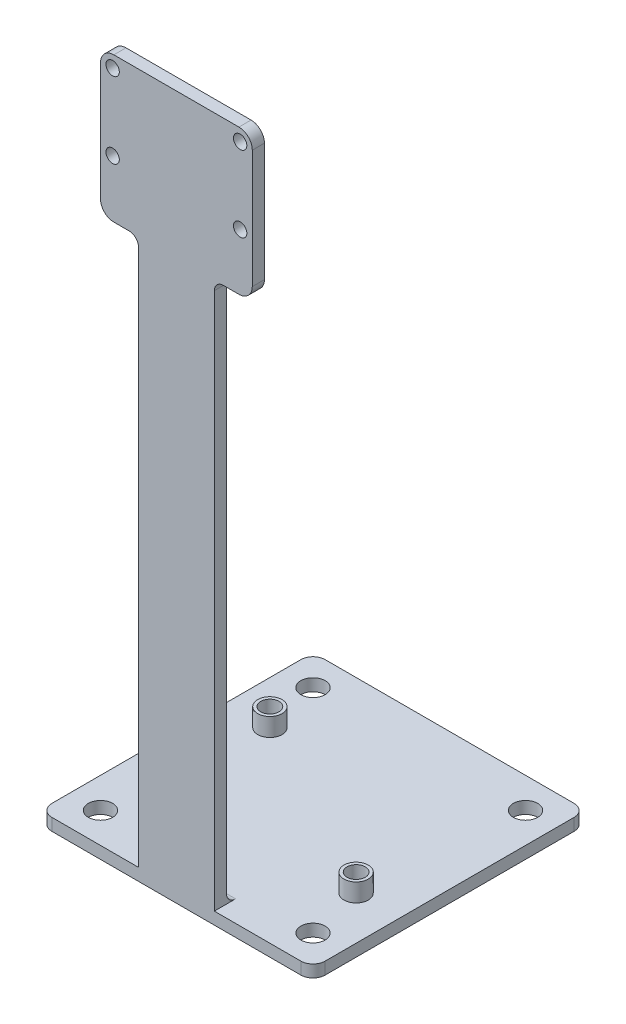
SolidWorks part; units mm, degrees
ref_plane "Front Plane" through (0, 0, 0) normal (0, 0, 1) x (1, 0, 0)
ref_plane "Top Plane" through (0, 0, 0) normal (0, 1, 0) x (1, 0, 0)
ref_plane "Right Plane" through (0, 0, 0) normal (1, 0, 0) x (0, 0, -1)
sketch "Sketch1" plane through (0, 0, 0) normal (0, 0, 1) x (1, 0, 0)
  line L0 (6.25, 0) -> (6.25, -90)
  line L1 (0, 0) -> (6.25, 0)
  line L2 (0, 0) -> (0, 23.862)
  line L3 (0, 23.862) -> (25, 23.862)
  line L4 (25, 0) -> (25, 23.862)
  line L5 (18.75, 0) -> (18.75, -90)
  line L6 (18.75, 0) -> (25, 0)
  line L7 (6.25, -90) -> (18.75, -90)
  circle A2 centre (2, 21.862) radius 1.1
  circle A3 centre (23, 21.862) radius 1.1
  circle A4 centre (2, 9.362) radius 1.1
  circle A5 centre (23, 9.362) radius 1.1
  dimension "D3" = 2.2
  dimension "D4" = 2.2
  dimension "D7" = 2.2
  dimension "D10" = 2.2
  dimension "D1" = 25
  dimension "D2" = 23.862
  dimension "D5" = 2
  dimension "D6" = 2
  dimension "D8" = 2
  dimension "D9" = 2
  dimension "D11" = 14.5
  dimension "D12" = 90
  dimension "D13" = 90
  dimension "D14" = 12.5
  dimension "D15" = 6.25
extrude "Boss-Extrude1" add sketch "Sketch1" along normal blind 2
fillet "Fillet1" radius 2.2 1 edges at (0, 0, 1)
fillet "Fillet2" radius 2.2 1 edges at (0, 23.862, 1)
fillet "Fillet3" radius 2.2 1 edges at (25, 23.862, 1)
fillet "Fillet5" radius 2.2 1 edges at (25, 0, 1)
fillet "Fillet6" radius 1.5 1 edges at (18.75, 0, 1)
fillet "Fillet7" radius 1.5 1 edges at (6.25, 0, 1)
sketch "Sketch5" plane through (0, -90, 0) normal (0, -1, 0) x (1, 0, 0)
  line L0 (6.25, 2) -> (6.25, 0) construction
  line L1 (-10, 2) -> (35, 2)
  line L2 (-10, 2) -> (-10, -43)
  line L3 (-10, -43) -> (35, -43)
  line L4 (35, 2) -> (35, -43)
  line L5 (6.25, 0) -> (18.75, 0) construction
  line L6 (6.25, 2) -> (18.75, 2) construction
  circle A0 centre (-5, -3) radius 2
  circle A1 centre (-5, -38) radius 2
  circle A2 centre (30, -3) radius 2
  circle A3 centre (30, -38) radius 2
  point P4 (-10, -20.5)
  point P5 (35, -20.5)
  point P6 (12.5, 2)
  point P7 (0, 0)
  point P8 (6.25, 1)
  point P9 (12.5, 0)
  point P16 (0, 0)
  point P23 (0, 0)
  point P24 (0, 0)
  point P25 (0, 0)
  point P26 (12.9667, -5.2821)
  point P27 (17.2186, -7.336)
  point P28 (0, 0)
  point P29 (0, 0)
  point P30 (0, 0)
  point P33 (0, 0)
  point P34 (0, 0)
  point P35 (0, 0)
  point P36 (12.5, 2)
  point P37 (0, 0)
  dimension "D4" = 4
  dimension "D5" = 4
  dimension "D6" = 4
  dimension "D7" = 4
  dimension "D1" = 45
  dimension "D2" = 45
  dimension "D3" = 35
  dimension "D8" = 35
  dimension "D9" = 5
  dimension "D10" = 5
extrude "Boss-Extrude4" add sketch "Sketch5" along normal blind 2
fillet "Fillet17" radius 2 1 edges at (35, -91, 2)
fillet "Fillet18" radius 2 1 edges at (-10, -91, 2)
fillet "Fillet19" radius 2 1 edges at (-10, -91, -43)
fillet "Fillet20" radius 2 1 edges at (35, -91, -43)
fillet "Fillet21" radius 1.5 1 edges at (12.5, -90, 0)
sketch "Sketch7" plane through (0, -92, 0) normal (0, -1, 0) x (1, 0, 0)
  line L0 (33, 2) -> (-8, 2) construction
  line L1 (-9.5, -9.75) -> (34.5, -9.75)
  line L2 (-9.5, -9.75) -> (-9.5, -31.25)
  line L3 (-9.5, -31.25) -> (34.5, -31.25)
  line L4 (34.5, -9.75) -> (34.5, -31.25)
  line L5 (35, -41) -> (35, 0) construction
  line L6 (-2.85, -12.25) -> (27.85, -28.75) construction
  line L7 (-9.5, -20.5) -> (34.5, -20.5) construction
  circle A0 centre (-2.85, -12.25) radius 1.5
  circle A1 centre (27.85, -28.75) radius 1.5
  circle A2 centre (27.85, -28.75) radius 2
  circle A3 centre (-2.85, -12.25) radius 2
  circle A4 centre (27.85, -12.25) radius 2
  circle A5 centre (27.85, -12.25) radius 1.5
  circle A6 centre (-2.85, -28.75) radius 1.5
  circle A7 centre (-2.85, -28.75) radius 2
  point P5 (12.5, -9.75)
  point P8 (12.5, 2)
  point P11 (35, -20.5)
  point P12 (-9.5, -20.5)
  dimension "D3" = 3
  dimension "D4" = 3
  dimension "D6" = 4
  dimension "D7" = 4
  dimension "D11" = 3
  dimension "D12" = 4
  dimension "D15" = 3
  dimension "D16" = 4
  dimension "D1" = 21.5
  dimension "D2" = 44
  dimension "D5" = 6.65
  dimension "D8" = 2.5
  dimension "D9" = 2.5
  dimension "D10" = 6.65
  dimension "D13" = 6.65
  dimension "D14" = 2.5
  dimension "D17" = 6.65
  dimension "D18" = 2.5
extrude "Boss-Extrude8" add sketch "Sketch7" against normal blind 5 contours A7 | A4
sketch "Sketch10" plane through (0, -87, 0) normal (0, 1, 0) x (1, 0, 0)
  circle A0 centre (27.85, 12.25) radius 1.5
  circle A1 centre (-2.85, 28.75) radius 1.5
  dimension "D1" = 3
  dimension "D2" = 3
extrude "Cut-Extrude4" cut sketch "Sketch10" against normal through all
